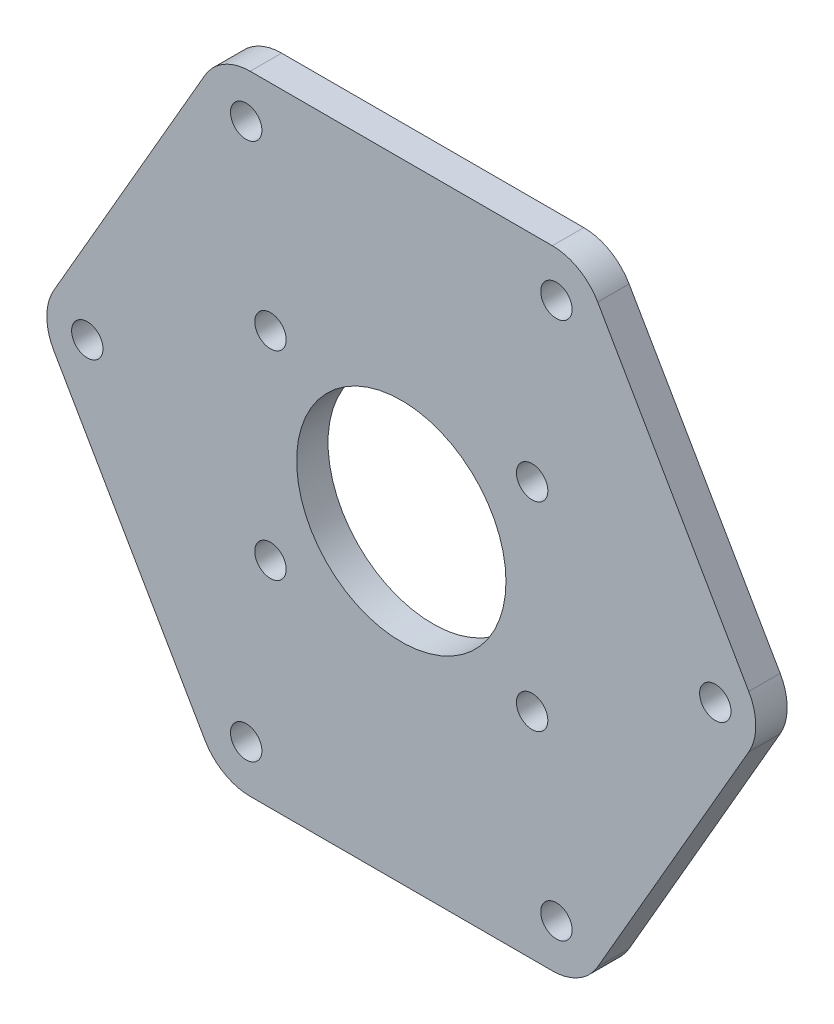
SolidWorks part; units mm, degrees
ref_plane "前视基准面" through (0, 0, 0) normal (0, 0, 1) x (1, 0, 0)
ref_plane "上视基准面" through (0, 0, 0) normal (0, 1, 0) x (1, 0, 0)
ref_plane "右视基准面" through (0, 0, 0) normal (1, 0, 0) x (0, 0, -1)
sketch "草图1" plane through (0, 0, 0) normal (0, 0, 1) x (1, 0, 0)
  line L1 (34.641, 0) -> (17.3205, 30)
  line L2 (17.3205, 30) -> (-17.3205, 30)
  line L3 (-17.3205, 30) -> (-34.641, 0)
  line L4 (-34.641, 0) -> (-17.3205, -30)
  line L5 (-17.3205, -30) -> (17.3205, -30)
  line L6 (17.3205, -30) -> (34.641, 0)
  circle A0 centre (0, 0) radius 30 construction
  dimension "D1" = 60
extrude "凸台-拉伸1" add sketch "草图1" along normal blind 3
sketch "草图2" plane through (0, 0, 3) normal (0, 0, 1) x (1, 0, 0)
  line L1 (-12.5, 9.5) -> (12.5, 9.5) construction
  line L2 (-12.5, 9.5) -> (-12.5, -9.5) construction
  line L3 (-12.5, -9.5) -> (12.5, -9.5) construction
  line L4 (12.5, 9.5) -> (12.5, -9.5) construction
  line L5 (-12.5, 9.5) -> (12.5, -9.5) construction
  line L6 (-12.5, -9.5) -> (12.5, 9.5) construction
  circle A0 centre (0, 0) radius 10
  circle A1 centre (-12.5, 9.5) radius 1.5
  circle A2 centre (12.5, 9.5) radius 1.5
  circle A3 centre (-12.5, -9.5) radius 1.5
  circle A4 centre (12.5, -9.5) radius 1.5
  dimension "D1" = 20
  dimension "D4" = 3
  dimension "D2" = 19
  dimension "D3" = 25
extrude "切除-拉伸1" cut sketch "草图2" against normal blind 3
sketch "草图3" plane through (0, 0, 3) normal (0, 0, 1) x (1, 0, 0)
  line L0 (-30, 0) -> (30, 0) construction
  line L2 (-90, 0) -> (90, 0) construction
  line L3 (0, 0) -> (-17.3205, -30) construction
  line L4 (0, 90) -> (0, -90) construction
  line L5 (0, 0) -> (17.3205, -30) construction
  line L6 (-17.3205, 30) -> (0, 0) construction
  line L7 (17.3205, 30) -> (0, 0) construction
  circle A0 centre (-30, 0) radius 1.5
  circle A1 centre (30, 0) radius 1.5
  circle A2 centre (-14.8205, -25.6699) radius 1.5
  circle A3 centre (14.8205, -25.6699) radius 1.5
  circle A4 centre (-14.8205, 25.6699) radius 1.5
  circle A5 centre (14.8205, 25.6699) radius 1.5
  point P3 (0, 0)
  dimension "D2" = 3
  dimension "D3" = 3
  dimension "D6" = 3
  dimension "D1" = 60
  dimension "D4" = 5
  dimension "D5" = 5
extrude "切除-拉伸2" cut sketch "草图3" against normal blind 3
fillet "圆角1" radius 5 6 edges at (34.641, 0, 1.5) (17.3205, 30, 1.5) (-17.3205, 30, 1.5) (-34.641, 0, 1.5) (-17.3205, -30, 1.5) (17.3205, -30, 1.5)
